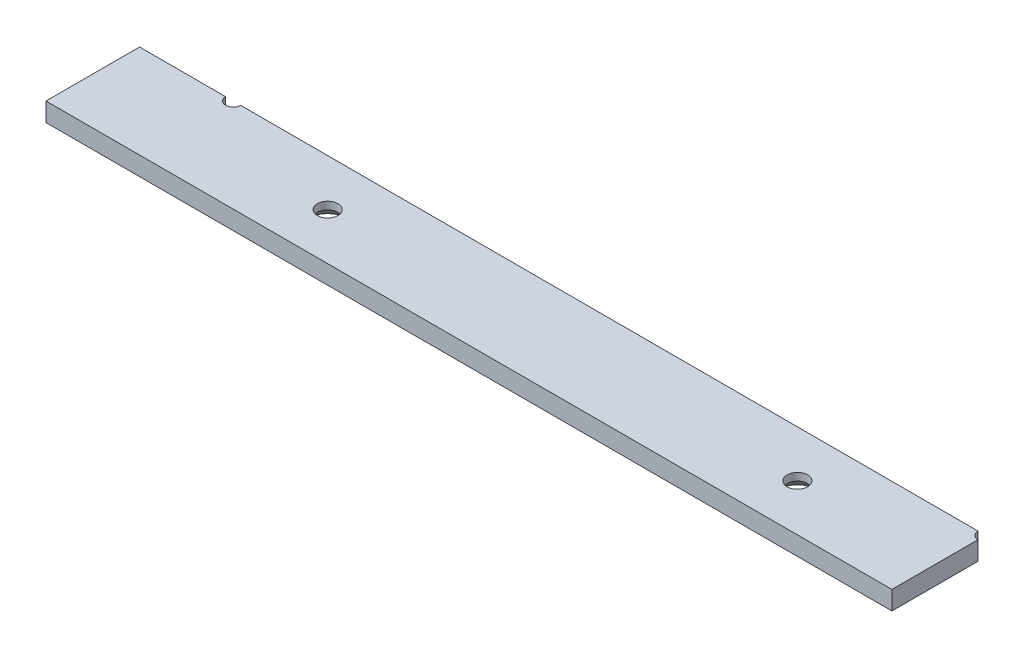
SolidWorks part; units mm, degrees
material "Acrílico (Impacto medio-alto)"
ref_plane "Alzado" through (0, 0, 0) normal (0, 0, 1) x (1, 0, 0)
ref_plane "Planta" through (0, 0, 0) normal (0, 1, 0) x (1, 0, 0)
ref_plane "Vista lateral" through (0, 0, 0) normal (1, 0, 0) x (0, 0, -1)
sketch "Croquis1" plane through (0, 0, 0) normal (0, 1, 0) x (1, 0, 0)
  line L1 (0, 0) -> (226, 0)
  line L2 (0, 0) -> (0, 25)
  line L3 (0, 25) -> (226, 25)
  line L4 (226, 0) -> (226, 25)
  dimension "D1" = 25
  dimension "D2" = 226
extrude "Saliente-Extruir1" add sketch "Croquis1" along normal blind 5
sketch "Croquis2" plane through (0, 5, 0) normal (0, 1, 0) x (1, 0, 0)
  line L0 (226, 25) -> (0, 25) construction
  line L2 (0, 25) -> (0, 0) construction
  circle A0 centre (25, 25) radius 2
  circle A1 centre (226, 25) radius 2
  dimension "D1" = 4
  dimension "D3" = 4
  dimension "D2" = 25
extrude "Cortar-Extruir1" cut sketch "Croquis2" against normal blind 5
sketch "Croquis3" plane through (0, 0, 0) normal (0, -1, 0) x (1, 0, 0)
  line L0 (125.5, 0) -> (125.5, -25) construction
  line L1 (0, 0) -> (226, 0) construction
  line L2 (224, -25) -> (27, -25) construction
  line L3 (0, -25) -> (0, 0) construction
  circle A0 centre (62.75, -12.5) radius 2.5
  circle A1 centre (188.25, -12.5) radius 2.5
  dimension "D2" = 5
  dimension "D1" = 125.5
  dimension "D3" = 62.75
hole_wizard "Avellanado para tornillo con cabeza avellanada de clavija hexagonal de M51" positions "Croquis5" profile "Croquis4" countersink size "M5" standard "DIN"
sketch "Croquis5" plane through (0, 0, 0) normal (0, -1, 0) x (-1, 0, 0)
  point P0 (-62.75, 12.5)
  point P3 (-188.25, 12.5)
sketch "Croquis4" plane through (62.75, 0, -12.5) normal (1, 0, 0) x (0, 0, -1)
  line L0 (0, 0) -> (0, 6.6524)
  line L1 (0, 6.6524) -> (2.75, 5)
  line L2 (2.75, 5) -> (2.75, 2.985)
  line L3 (2.75, 2.985) -> (5.735, 0)
  line L5 (5.735, 0) -> (0, 0)
  line L6 (-2.75, 2.985) -> (-5.735, 0) construction
  line L10 (0, 6.6524) -> (-2.75, 5) construction
  line L11 (0, -6.35) -> (0, 107.95) construction
  dimension "Diámetro de taladro" = 5.5
  dimension "Profundidad de taladro" = 5
  dimension "Ángulo de avellanado cercano" = 11.47
  dimension "Ángulo de avellanado lejano" = 90
  dimension "Ángulo de perforador" = 118
